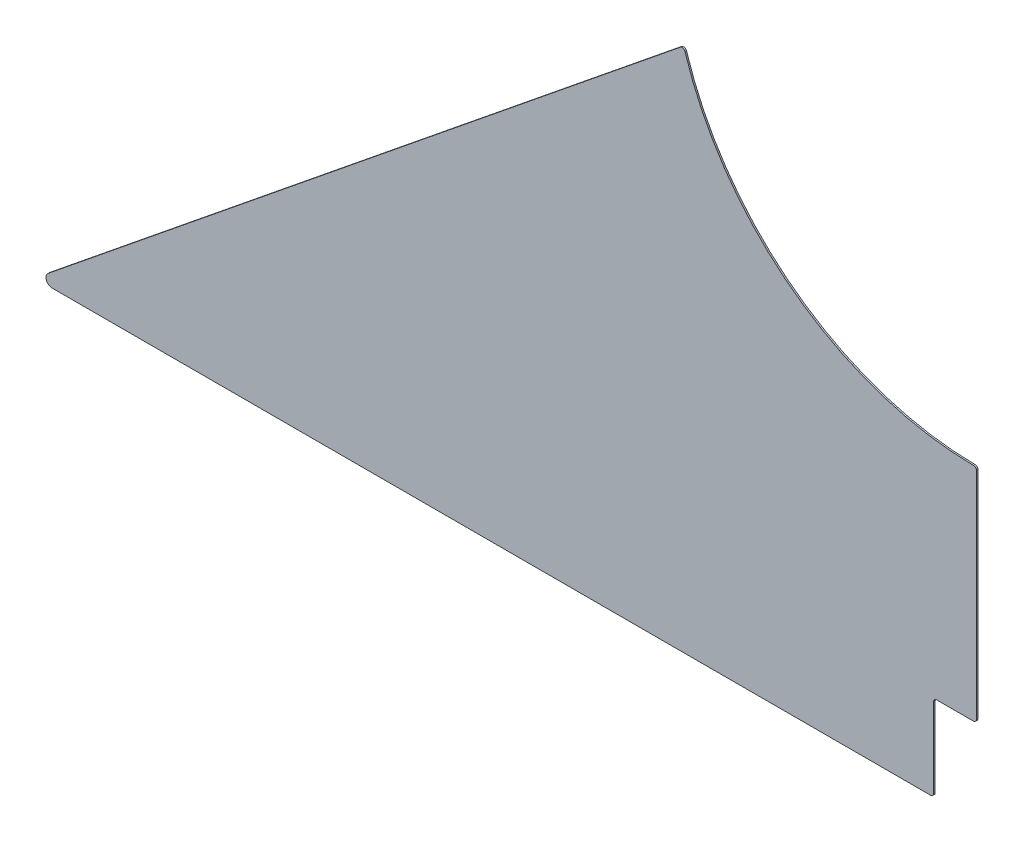
SolidWorks part; units mm, degrees
material "PC High Viscosity"
ref_plane "Front Plane" through (0, 0, 0) normal (0, 0, 1) x (1, 0, 0)
ref_plane "Top Plane" through (0, 0, 0) normal (0, 1, 0) x (1, 0, 0)
ref_plane "Right Plane" through (0, 0, 0) normal (1, 0, 0) x (0, 0, -1)
sketch "Sketch1" plane through (0, 0, 0) normal (0, 0, 1) x (1, 0, 0)
  line L0 (1292.225, 0) -> (-1292.225, 0)
  line L1 (-1292.225, 0) -> (-304.3036, 800.003)
  line L2 (0, 0) -> (0, 573.0875) construction
  line L3 (304.3036, 800.003) -> (1292.225, 0)
  arc A0 (-304.3036, 800.003) -> (304.3036, 800.003) centre (0, 890.5875) ccw
  point P4 (0, 0)
  point P10 (0, 573.0875)
  dimension "D4" = 317.5
  dimension "D1" = 1292.225
  dimension "D2" = 39
  dimension "D3" = 573.0875
extrude "Boss-Extrude1" add sketch "Sketch1" along normal blind 1.5875
sketch "Sketch2" plane through (0, 0, 1.5875) normal (0, 0, 1) x (1, 0, 0)
  line L0 (-1292.225, 0) -> (1292.225, 0) construction
  line L1 (-44.45, 0) -> (44.45, 0)
  line L2 (-44.45, 0) -> (-44.45, 342.9)
  line L3 (-44.45, 342.9) -> (44.45, 342.9)
  line L4 (44.45, 0) -> (44.45, 342.9)
  point P6 (0, 342.9)
  dimension "D1" = 342.9
  dimension "D2" = 88.9
extrude "Cut-Extrude1" cut sketch "Sketch2" against normal through all
sketch "Sketch4" plane through (0, 0, 1.5875) normal (0, 0, 1) x (1, 0, 0)
  line L1 (1292.225, 0) -> (0, 0)
  line L2 (1292.225, 0) -> (1292.225, 800.003)
  line L3 (1292.225, 800.003) -> (0, 800.003)
  line L4 (0, 0) -> (0, 800.003)
extrude "Cut-Extrude2" cut sketch "Sketch4" against normal through all
sketch "Sketch5" plane through (0, 0, 1.5875) normal (0, 0, 1) x (1, 0, 0)
  line L0 (-44.45, 253.903) -> (-978.681, 253.903)
  line L1 (-44.45, 342.9) -> (-44.45, 0) construction
  line L2 (-304.3036, 800.003) -> (-1292.225, 0) construction
  line L3 (-978.681, 253.903) -> (-1292.225, 0)
  line L4 (-1292.225, 0) -> (-44.45, 0)
  line L5 (-44.45, 0) -> (-44.45, 253.903)
  line L6 (-883.412, 253.903) -> (-883.412, 331.0502) construction
  line L7 (0, 573.0875) -> (0, 342.9) construction
  dimension "D1" = 546.1
  dimension "D2" = 978.681
  dimension "D3" = 883.412
extrude "Cut-Extrude3" cut sketch "Sketch5" against normal through all
fillet "Fillet1" radius 3.175 5 edges at (0, 573.0875, 0.7937) (-44.45, 342.9, 0.7937) (0, 342.9, 0.7937) (-44.45, 253.903, 0.7937) (-304.3036, 800.003, 0.7937)
fillet "Fillet2" radius 6.35 1 edges at (-978.681, 253.903, 0.7937)
